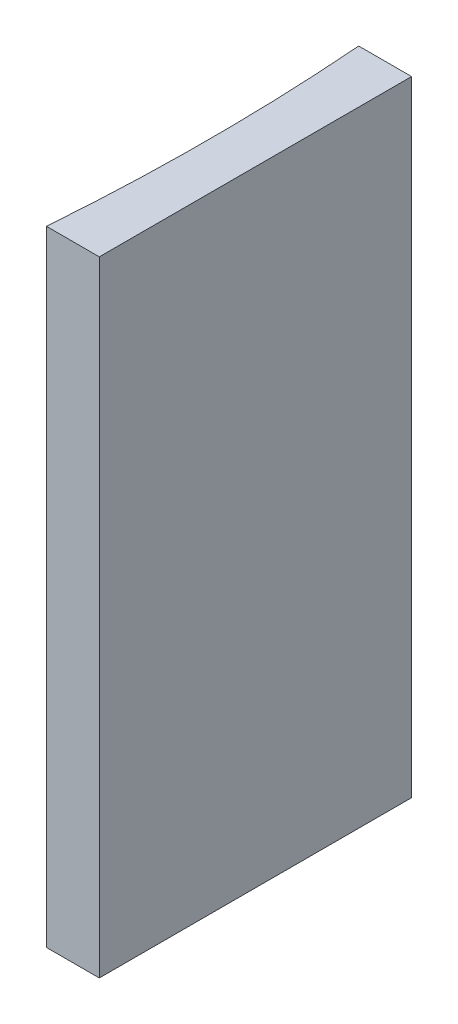
SolidWorks part; units mm, degrees
ref_plane "前视基准面" through (0, 0, 0) normal (0, 0, 1) x (1, 0, 0)
ref_plane "上视基准面" through (0, 0, 0) normal (0, 1, 0) x (1, 0, 0)
ref_plane "右视基准面" through (0, 0, 0) normal (1, 0, 0) x (0, 0, -1)
sketch "草图1" plane through (0, 0, 0) normal (0, 1, 0) x (1, 0, 0)
  line L0 (0, 0) -> (0, -20)
  line L1 (0, 0) -> (-3.3874, 0)
  line L2 (0, -20) -> (-3.3874, -20)
  line L3 (8.2336, -10) -> (-10.4405, -10) construction
  arc A0 (-3.3874, -20) -> (-3.3874, 0) centre (-132.25, -10) ccw
  point P7 (-3, -10)
  point P8 (0, -10)
  dimension "D2" = 129.25
  dimension "D3" = 3
  dimension "D1" = 20
extrude "凸台-拉伸1" add sketch "草图1" along normal blind 40
